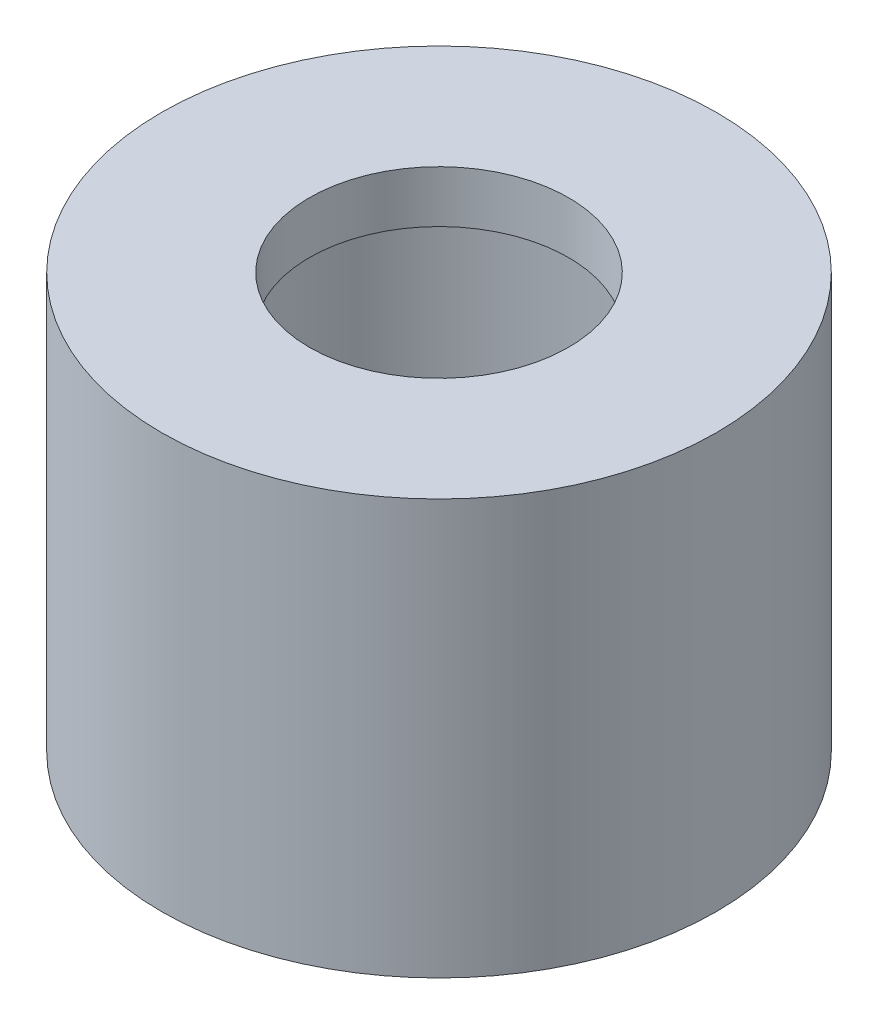
SolidWorks part; units mm, degrees
ref_plane "前视基准面" through (0, 0, 0) normal (0, 0, 1) x (1, 0, 0)
ref_plane "上视基准面" through (0, 0, 0) normal (0, 1, 0) x (1, 0, 0)
ref_plane "右视基准面" through (0, 0, 0) normal (1, 0, 0) x (0, 0, -1)
sketch "草图1" plane through (0, 0, 0) normal (0, 1, 0) x (1, 0, 0)
  circle A0 centre (0, 0) radius 4
  circle A1 centre (0, 0) radius 5.35
  dimension "D1" = 8
  dimension "D2" = 10.7
extrude "凸台-拉伸1" add sketch "草图1" along normal blind 3
sketch "草图2" plane through (0, 0, 0) normal (0, -1, 0) x (1, 0, 0)
  circle A0 centre (0, 0) radius 4
  circle A1 centre (0, 0) radius 5.35
extrude "凸台-拉伸2" add sketch "草图2" along normal blind 5
sketch "草图3" plane through (0, 3, 0) normal (0, 1, 0) x (1, 0, 0)
  circle A0 centre (0, 0) radius 4
extrude "凸台-拉伸3" add sketch "草图3" against normal blind 1
sketch "草图4" plane through (0, 3, 0) normal (0, 1, 0) x (1, 0, 0)
  circle A0 centre (0, 0) radius 2.5
  dimension "D1" = 5
extrude "切除-拉伸1" cut sketch "草图4" against normal blind 1
